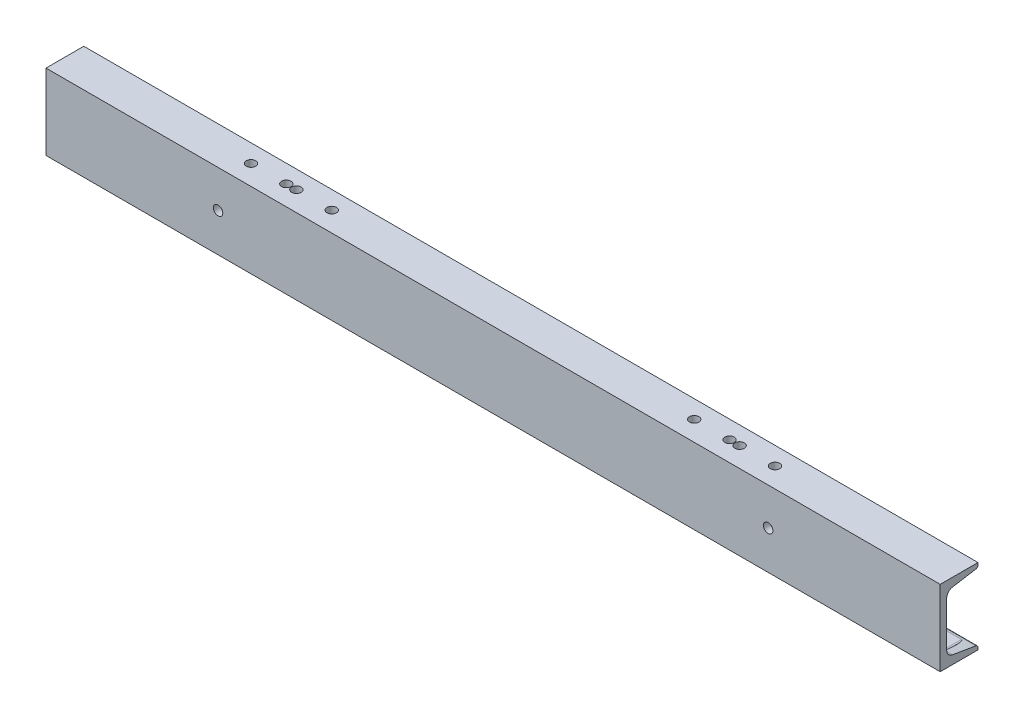
SolidWorks part; units mm, degrees
material "Plain Carbon Steel"
ref_plane "Front Plane" through (0, 0, 0) normal (0, 0, 1) x (1, 0, 0)
ref_plane "Top Plane" through (0, 0, 0) normal (0, 1, 0) x (1, 0, 0)
ref_plane "Right Plane" through (0, 0, 0) normal (1, 0, 0) x (0, 0, -1)
sketch "Sketch1" plane through (0, 0, 0) normal (0, 1, 0) x (1, 0, 0)
  line L0 (-450, 0) -> (450, 0)
  dimension "D1" = 900
other "Structural Member1"
ref_plane "Plane1" through (-450, 0, 0) normal (1, 0, 0) x (0, 0, -1)
sketch "Sketch11" plane through (-450, 0, 0) normal (1, 0, 0) x (0, 0, -1)
  line L0 (0, -38.1) -> (0, 38.1)
  line L1 (0, 38.1) -> (38.0492, 38.1)
  line L2 (0, -38.1) -> (38.0492, -38.1)
  line L5 (31.75, -31.1658) -> (6.35, -31.1658) construction
  line L6 (0, 0) -> (6.5532, 0) construction
  line L12 (6.5532, 22.7314) -> (6.5532, -22.7314)
  line L15 (38.0492, 38.1) -> (38.0492, 35.9423)
  line L16 (38.0492, -38.1) -> (38.0492, -35.9423)
  line L17 (12.2837, 29.4961) -> (35.9268, 33.4369)
  line L18 (12.2837, -29.4961) -> (35.9268, -33.4369)
  arc A9 (6.5532, -22.7314) -> (12.2837, -29.4961) centre (13.4112, -22.7314) ccw
  arc A10 (6.5532, 22.7314) -> (12.2837, 29.4961) centre (13.4112, 22.7314) cw
  arc A11 (38.0492, 35.9423) -> (35.9268, 33.4369) centre (35.5092, 35.9423) cw
  arc A12 (38.0492, -35.9423) -> (35.9268, -33.4369) centre (35.5092, -35.9423) ccw
  point P4 (38.0492, 33.7907)
  point P5 (38.0492, -33.7907)
  point P6 (3.2766, 0)
  point P7 (19.0246, 38.1)
  point P12 (19.0246, -38.1)
  point P13 (0, 0)
  dimension "RI" = 6.858
  dimension "D2" = 9.463
  dimension "RA" = 2.54
  dimension "Depth" = 76.2
  dimension "BF" = 38.0492
  dimension "TW" = 6.5532
  dimension "flange" = 2.1577
  dimension "TF" = 6.9342
sketch "Sketch12" plane through (0, 0, 0) normal (0, 1, 0) x (1, 0, 0)
  line L0 (-412.5239, 20) -> (413.742, 20) construction
  line L1 (-450, 0) -> (450, 0) construction
  line L2 (0, 0) -> (0, 45.9021) construction
  line L3 (-450, 38.0492) -> (-450, 0) construction
  circle A0 centre (-425, 20) radius 4.7625
  circle A1 centre (425, 20) radius 4.7625
  dimension "D2" = 9.525
  dimension "D1" = 20
  dimension "D3" = 25
extrude "Cut-Extrude1" cut sketch "Sketch12" against normal through all
sketch "Sketch15" plane through (0, 0, -6.5532) normal (0, 0, -1) x (-1, 0, 0)
  line L0 (-425, -21.1359) -> (-425, -40.4286) construction
  line L1 (-375.1366, -28.1) -> (-474.8634, -28.1) construction
  line L2 (-450, -38.1) -> (450, -38.1) construction
  line L3 (-412.5, -28.1) -> (-437.5, -28.1) construction
  line L4 (-412.5, -33.1) -> (-437.5, -33.1)
  line L5 (-412.5, -23.1) -> (-437.5, -23.1)
  line L6 (0, 0) -> (0, -58.1771) construction
  line L7 (412.5, -28.1) -> (437.5, -28.1) construction
  line L8 (412.5, -33.1) -> (437.5, -33.1)
  line L9 (412.5, -23.1) -> (437.5, -23.1)
  arc A0 (-412.5, -33.1) -> (-412.5, -23.1) centre (-412.5, -28.1) ccw
  arc A1 (-437.5, -23.1) -> (-437.5, -33.1) centre (-437.5, -28.1) ccw
  arc A2 (412.5, -33.1) -> (412.5, -23.1) centre (412.5, -28.1) cw
  arc A3 (437.5, -23.1) -> (437.5, -33.1) centre (437.5, -28.1) cw
  ellipse E0 centre (-425, -30.7822) end of major axis (-429.7625, -30.7822) minor radius 0.7938 construction
  point P0 (-425, -30.7822)
  point P11 (-425, -28.1)
  point P16 (-425, -28.1)
  point P26 (425, -28.1)
  dimension "D2" = 5
  dimension "D1" = 10
  dimension "D3" = 25
extrude "Cut-Extrude2" cut sketch "Sketch15" along normal blind 40
sketch "Sketch16" plane through (0, 0, 0) normal (0, 1, 0) x (1, 0, 0)
  line L0 (0, -46.4014) -> (0, 86.4014) construction
  line L1 (-394.0256, 20) -> (394.0256, 20) construction
  line L2 (450, 0) -> (-450, 0) construction
  circle A0 centre (-263.7, 20) radius 4.7625
  circle A1 centre (-228.1, 20) radius 4.7625
  circle A2 centre (228.1, 20) radius 4.7625
  circle A3 centre (263.7, 20) radius 4.7625
  circle A4 centre (-218, 20) radius 4.7625
  circle A5 centre (-182.4, 20) radius 4.7625
  circle A6 centre (182.4, 20) radius 4.7625
  circle A7 centre (218, 20) radius 4.7625
  point P5 (0, 20)
  point P6 (0, 20)
  dimension "D2" = 9.525
  dimension "D1" = 20
  dimension "D3" = 263.7
  dimension "D4" = 35.6
  dimension "D5" = 218
  dimension "D6" = 35.6
extrude "Cut-Extrude3" cut sketch "Sketch16" along normal through all
sketch "Sketch17" plane through (0, 0, 0) normal (0, 0, 1) x (1, 0, 0)
  circle A0 centre (276.8375, 0.6) radius 4.7625 construction
  circle A1 centre (-276.8375, 0.6) radius 4.7625 construction
  circle A2 centre (276.8375, 0.6) radius 4.7625
  circle A3 centre (-276.8375, 0.6) radius 4.7625
extrude "Cut-Extrude4" cut sketch "Sketch17" against normal through all
